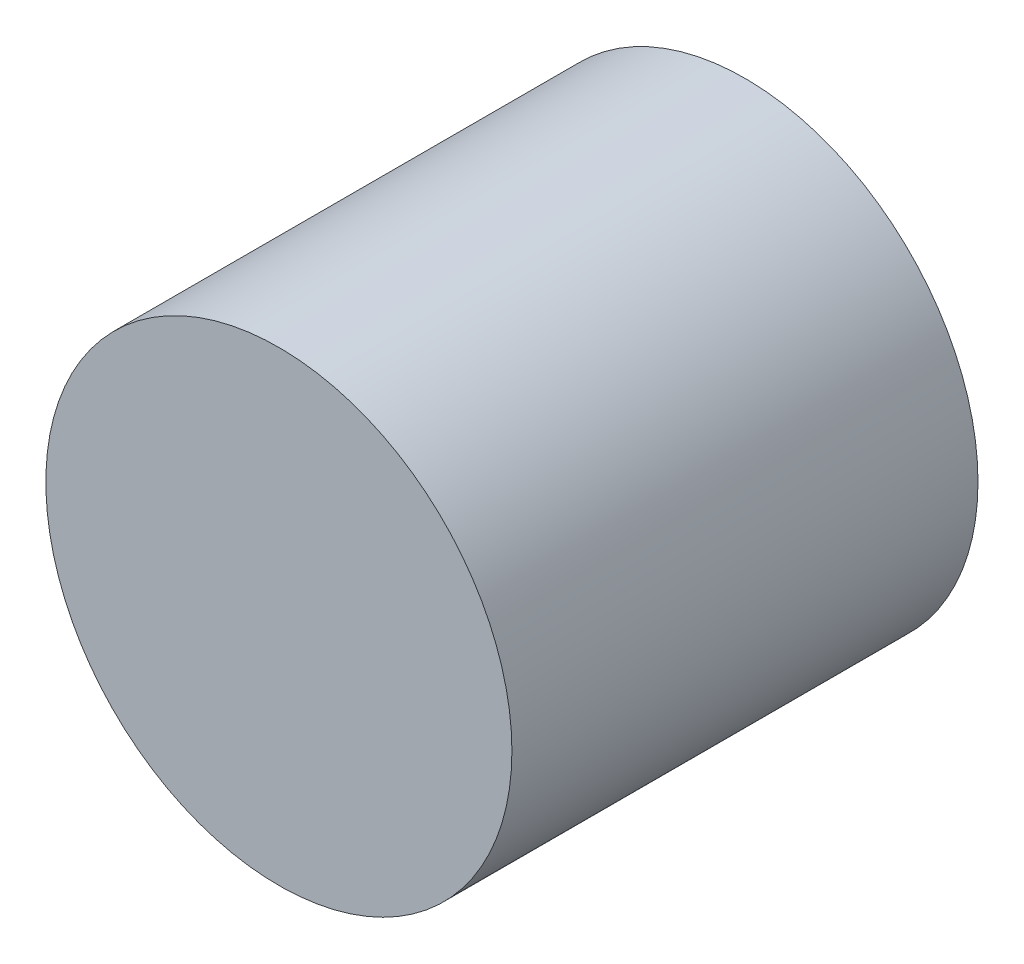
SolidWorks part; units mm, degrees
ref_plane "Front Plane" through (0, 0, 0) normal (0, 0, 1) x (1, 0, 0)
ref_plane "Top Plane" through (0, 0, 0) normal (0, 1, 0) x (1, 0, 0)
ref_plane "Right Plane" through (0, 0, 0) normal (1, 0, 0) x (0, 0, -1)
sketch "Sketch1" plane through (0, 0, 0) normal (0, 0, 1) x (1, 0, 0)
  circle A0 centre (0, 0) radius 5
extrude "Boss-Extrude1" add sketch "Sketch1" along normal blind 10
